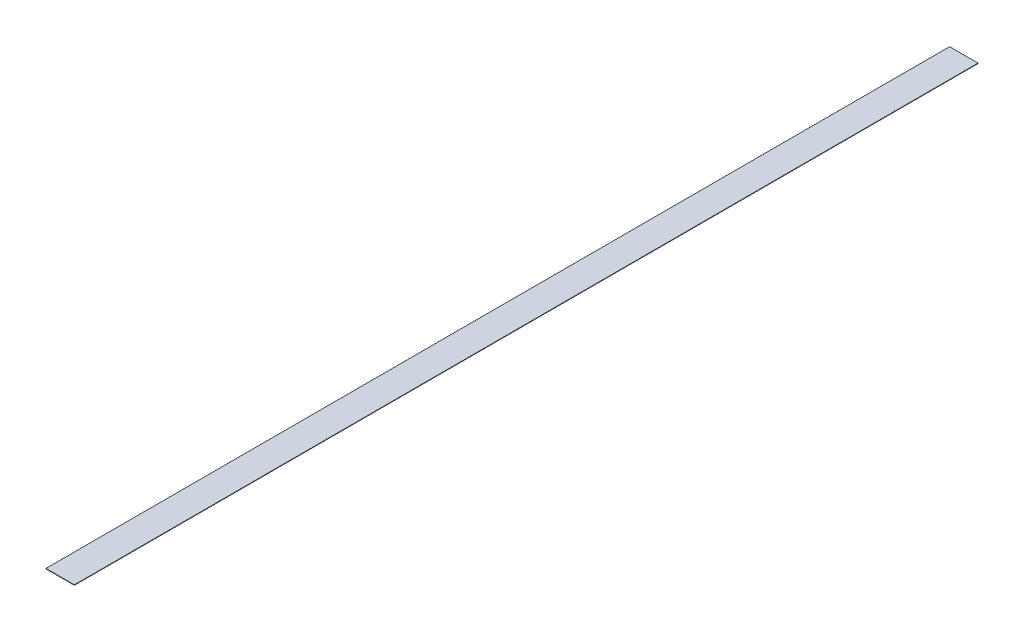
SolidWorks part; units mm, degrees
material "Silicon Rubber"
ref_plane "Front Plane" through (0, 0, 0) normal (0, 0, 1) x (1, 0, 0)
ref_plane "Top Plane" through (0, 0, 0) normal (0, 1, 0) x (1, 0, 0)
ref_plane "Right Plane" through (0, 0, 0) normal (1, 0, 0) x (0, 0, -1)
sketch "Sketch1" plane through (0, 0, 0) normal (0, 1, 0) x (1, 0, 0)
  line L1 (-25.4, 808.0375) -> (25.4, 808.0375)
  line L2 (-25.4, 808.0375) -> (-25.4, -808.0375)
  line L3 (-25.4, -808.0375) -> (25.4, -808.0375)
  line L4 (25.4, 808.0375) -> (25.4, -808.0375)
  line L5 (-25.4, 808.0375) -> (25.4, -808.0375) construction
  line L6 (-25.4, -808.0375) -> (25.4, 808.0375) construction
  point P0 (0, 0)
  dimension "D1" = 50.8
  dimension "D2" = 1616.075
extrude "Boss-Extrude1" add sketch "Sketch1" along normal blind 0.7937
